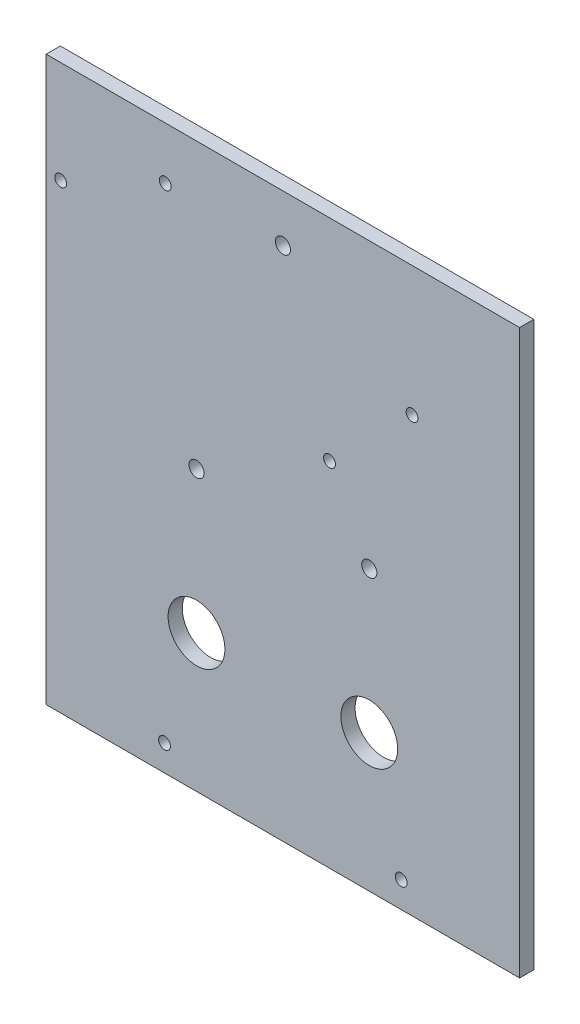
SolidWorks part; units mm, degrees
ref_plane "正面" through (0, 0, 0) normal (0, 0, 1) x (1, 0, 0)
ref_plane "平面" through (0, 0, 0) normal (0, 1, 0) x (1, 0, 0)
ref_plane "右側面" through (0, 0, 0) normal (1, 0, 0) x (0, 0, -1)
sketch "ｽｹｯﾁ1" plane through (0, 0, 0) normal (0, 0, 1) x (1, 0, 0)
  line L1 (-50, 60) -> (50, 60)
  line L2 (-50, 60) -> (-50, -60)
  line L3 (-50, -60) -> (50, -60)
  line L4 (50, 60) -> (50, -60)
  line L5 (-50, 60) -> (50, -60) construction
  line L6 (-50, -60) -> (50, 60) construction
  circle A0 centre (-46.9555, 38.4899) radius 1.7
  circle A1 centre (-24.84, 48.97) radius 1.6
  circle A2 centre (9.8382, 15.4687) radius 1.6
  circle A3 centre (27.3238, 32.5914) radius 1.6
  point P0 (0, 0)
  dimension "D3" = 3.2
  dimension "D4" = 3.2
  dimension "D5" = 3.2
  dimension "D6" = 3.4
  dimension "D1" = 100
  dimension "D2" = 120
extrude "ﾎﾞｽ - 押し出し1" add sketch "ｽｹｯﾁ1" along normal blind 3 contours A0 | L4 L1 L2 L3 A3 A2 A1 A0 | A1 | A2 | A3
sketch "ｽｹｯﾁ2" plane through (0, 0, 3) normal (0, 0, 1) x (1, 0, 0)
  line L0 (0, -60) -> (0, -30)
  line L1 (-50, -60) -> (50, -60) construction
  line L2 (0, -30) -> (-18.25, -30)
  line L3 (0, -30) -> (18.25, -30)
  circle A0 centre (18.25, -30) radius 6
  circle A1 centre (-18.25, -30) radius 6
  dimension "D4" = 12
  dimension "D5" = 12
  dimension "D1" = 30
  dimension "D2" = 18.25
  dimension "D3" = 18.25
extrude "ｶｯﾄ - 押し出し1" cut sketch "ｽｹｯﾁ2" against normal blind 3
sketch "ｽｹｯﾁ3" plane through (0, 0, 3) normal (0, 0, 1) x (1, 0, 0)
  line L0 (18.25, -30) -> (18.25, 0)
  line L1 (-18.25, -30) -> (-18.25, 0)
  circle A0 centre (18.25, 0) radius 1.6
  circle A1 centre (-18.25, 0) radius 1.6
  dimension "D3" = 3.2
  dimension "D4" = 3.2
  dimension "D1" = 30
  dimension "D2" = 30
extrude "ｶｯﾄ - 押し出し2" cut sketch "ｽｹｯﾁ3" against normal blind 3
sketch "ｽｹｯﾁ4" plane through (0, 0, 3) normal (0, 0, 1) x (1, 0, 0)
  line L0 (0, -60) -> (0, -53.5)
  line L1 (-50, -60) -> (50, -60) construction
  line L2 (0, -53.5) -> (-25, -53.5)
  line L3 (0, -53.5) -> (25, -53.5)
  circle A0 centre (-25, -53.5) radius 1.6
  circle A1 centre (25, -53.5) radius 1.6
  dimension "D4" = 3.2
  dimension "D5" = 3.2
  dimension "D1" = 6.5
  dimension "D2" = 25
  dimension "D3" = 25
sketch "ｽｹｯﾁ5" plane through (0, 0, 3) normal (0, 0, 1) x (1, 0, 0)
  line L0 (0, 60) -> (0, 50)
  line L1 (50, 60) -> (-50, 60) construction
  circle A0 centre (0, 50) radius 1.6
  dimension "D2" = 3.2
  dimension "D1" = 10
extrude "ｶｯﾄ - 押し出し4" cut sketch "ｽｹｯﾁ5" against normal blind 10
sketch "ｽｹｯﾁ6" plane through (0, -60, 0) normal (0, -1, 0) x (-1, 0, 0)
  line L1 (-50, -3) -> (50, -3)
  line L2 (-50, -3) -> (-50, 0)
  line L3 (-50, 0) -> (50, 0)
  line L4 (50, -3) -> (50, 0)
extrude "ｶｯﾄ - 押し出し5" cut sketch "ｽｹｯﾁ6" against normal blind 1
hole_wizard "M3x0.5 ねじ穴1" positions "3Dｽｹｯﾁ1" profile "ｽｹｯﾁ7" tap size "M3x0.5" standard "JIS"
sketch3d "3Dｽｹｯﾁ1"
  point P0 (-25, -53.5, 3)
  point P3 (25, -53.5, 3)
sketch "ｽｹｯﾁ7" plane through (-25, -53.5, 3) normal (1, 0, 0) x (0, -1, 0)
  line L0 (0, 0) -> (0, 9.2511)
  line L1 (0, 9.2511) -> (1.25, 8.5)
  line L2 (1.25, 8.5) -> (1.25, 0)
  line L5 (1.25, 0) -> (0, 0)
  line L10 (0, 9.2511) -> (-1.25, 8.5) construction
  line L11 (0, -6.35) -> (0, 107.95) construction
  dimension "ねじ下穴ﾄﾞﾘﾙ直径" = 2.5
  dimension "ねじ下穴ﾄﾞﾘﾙの深さ" = 8.5
  dimension "ﾄﾞﾘﾙ角度" = 118
hole_wizard "M3x0.5 ねじ穴2" positions "3Dｽｹｯﾁ3" profile "ｽｹｯﾁ9" tap size "M3x0.5" standard "JIS"
sketch3d "3Dｽｹｯﾁ3"
  point P0 (-24.8531, 48.954, 0)
  point P2 (-46.9555, 38.4899, 0)
  point P5 (27.3238, 32.5914, 0)
  point P8 (9.8382, 15.4687, 0)
  point P11 (27.2853, 32.6288, 0)
  point P13 (9.8437, 15.5107, 0)
  point P15 (-46.9398, 38.4479, 0)
sketch "ｽｹｯﾁ9" plane through (-24.8531, 48.954, 0) normal (1, 0, 0) x (0, 1, 0)
  line L0 (0, 0) -> (0, 9.2511)
  line L1 (0, 9.2511) -> (1.25, 8.5)
  line L2 (1.25, 8.5) -> (1.25, 0)
  line L5 (1.25, 0) -> (0, 0)
  line L10 (0, 9.2511) -> (-1.25, 8.5) construction
  line L11 (0, -6.35) -> (0, 107.95) construction
  dimension "ねじ下穴ﾄﾞﾘﾙ直径" = 2.5
  dimension "ねじ下穴ﾄﾞﾘﾙの深さ" = 8.5
  dimension "ﾄﾞﾘﾙ角度" = 118
cosmetic thread "穴のねじ山3" parameters "D1"=3, "D2"=3
cosmetic thread "穴のねじ山4" parameters "D1"=3, "D2"=3
cosmetic thread "穴のねじ山5" parameters "D1"=3, "D2"=3
cosmetic thread "穴のねじ山6" parameters "D1"=3, "D2"=3
cosmetic thread "穴のねじ山7" parameters "D1"=3, "D2"=3
cosmetic thread "穴のねじ山8" parameters "D1"=3, "D2"=3
cosmetic thread "穴のねじ山9" parameters "D1"=3, "D2"=3
hole_wizard "M3x0.5 ねじ穴4" positions "3Dｽｹｯﾁ5" profile "ｽｹｯﾁ11" tap size "M3x0.5" standard "JIS"
sketch3d "3Dｽｹｯﾁ5"
  point P0 (-25, -53.5, 3)
  point P3 (25, -53.5, 3)
  point P6 (24.9945, -53.5142, 3)
  point P8 (-25, -53.5, 3)
sketch "ｽｹｯﾁ11" plane through (-25, -53.5, 3) normal (1, 0, 0) x (0, -1, 0)
  line L0 (0, 0) -> (0, 9.2511)
  line L1 (0, 9.2511) -> (1.25, 8.5)
  line L2 (1.25, 8.5) -> (1.25, 0)
  line L5 (1.25, 0) -> (0, 0)
  line L10 (0, 9.2511) -> (-1.25, 8.5) construction
  line L11 (0, -6.35) -> (0, 107.95) construction
  dimension "ねじ下穴ﾄﾞﾘﾙ直径" = 2.5
  dimension "ねじ下穴ﾄﾞﾘﾙの深さ" = 8.5
  dimension "ﾄﾞﾘﾙ角度" = 118
cosmetic thread "穴のねじ山15" parameters "D1"=3, "D2"=3
cosmetic thread "穴のねじ山16" parameters "D1"=3, "D2"=3
cosmetic thread "穴のねじ山17" parameters "D1"=3, "D2"=3
cosmetic thread "穴のねじ山18" parameters "D1"=3, "D2"=3
